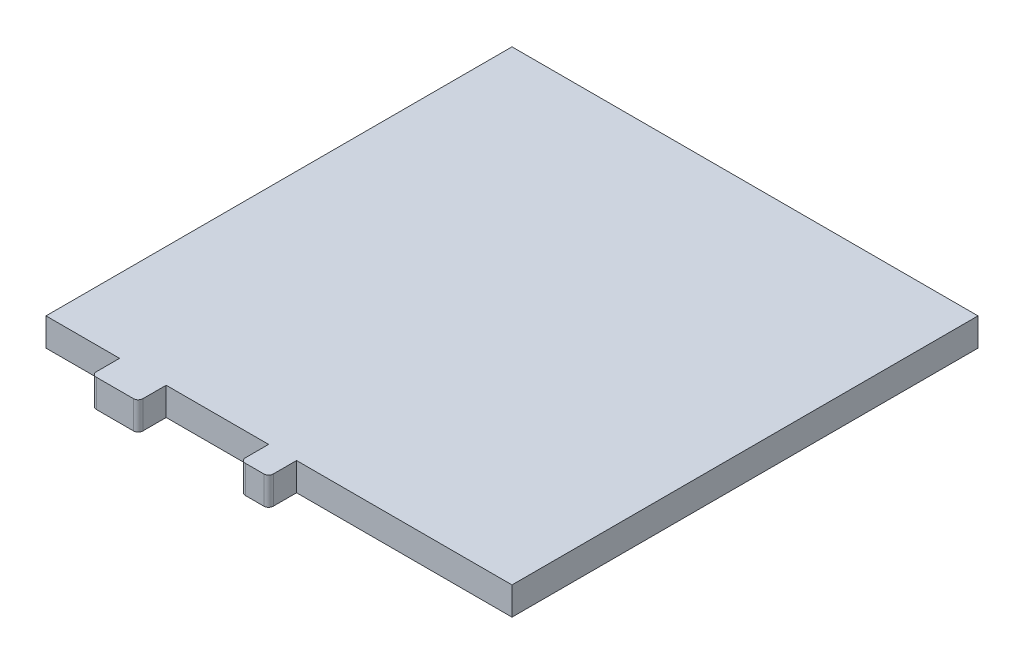
SolidWorks part; units mm, degrees
material "Maple"
ref_plane "Front Plane" through (0, 0, 0) normal (0, 0, 1) x (1, 0, 0)
ref_plane "Top Plane" through (0, 0, 0) normal (0, 1, 0) x (1, 0, 0)
ref_plane "Right Plane" through (0, 0, 0) normal (1, 0, 0) x (0, 0, -1)
sketch "Sketch1" plane through (0, 0, 0) normal (0, 1, 0) x (1, 0, 0)
  line L1 (-50, 50) -> (50, 50)
  line L2 (-50, 50) -> (-50, -50)
  line L3 (-50, -50) -> (50, -50)
  line L4 (50, 50) -> (50, -50)
  line L5 (-50, 50) -> (50, -50) construction
  line L6 (-50, -50) -> (50, 50) construction
  point P0 (0, 0)
  dimension "D1" = 100
extrude "Boss-Extrude1" add sketch "Sketch1" along normal blind 6
ref_plane "Plane1" through (0, 3, 0) normal (0, 1, 0) x (1, 0, 0)
sketch "Sketch234" plane through (0, 0, 50) normal (0, 0, 1) x (1, 0, 0)
  line L1 (-2.2322, 6) -> (3.7678, 6)
  line L2 (-2.2322, 6) -> (-2.2322, 0)
  line L3 (-2.2322, 0) -> (3.7678, 0)
  line L4 (3.7678, 6) -> (3.7678, 0)
  line L5 (-2.2322, 6) -> (3.7678, 0) construction
  line L6 (-2.2322, 0) -> (3.7678, 6) construction
  point P0 (0.7678, 3)
  dimension "tab_width" = 6
  dimension "D2" = 6
extrude "Boss-Extrude234" add sketch "Sketch234" along normal blind 6
fillet "Fillet134" radius 1 2 edges at (-2.2322, 3, 56) (3.7678, 3, 56)
sketch "Sketch2342" plane through (-28.4454, 6, 50) normal (0, 0, 1) x (-1, 0, 0)
  line L1 (-4.2322, 6) -> (5.7678, 6)
  line L2 (-4.2322, 6) -> (-4.2322, 0)
  line L3 (-4.2322, 0) -> (5.7678, 0)
  line L4 (5.7678, 6) -> (5.7678, 0)
  line L5 (-4.2322, 6) -> (5.7678, 0) construction
  line L6 (-4.2322, 0) -> (5.7678, 6) construction
  point P0 (0.7678, 3)
  dimension "D1" = 10
  dimension "D2" = 6
extrude "Boss-Extrude2342" add sketch "Sketch2342" along normal blind 6
fillet "Fillet1342" radius 1 2 edges at (-24.2132, 3, 56) (-34.2132, 3, 56)
other "Smart-Feature2<virtual_pin-3>"
